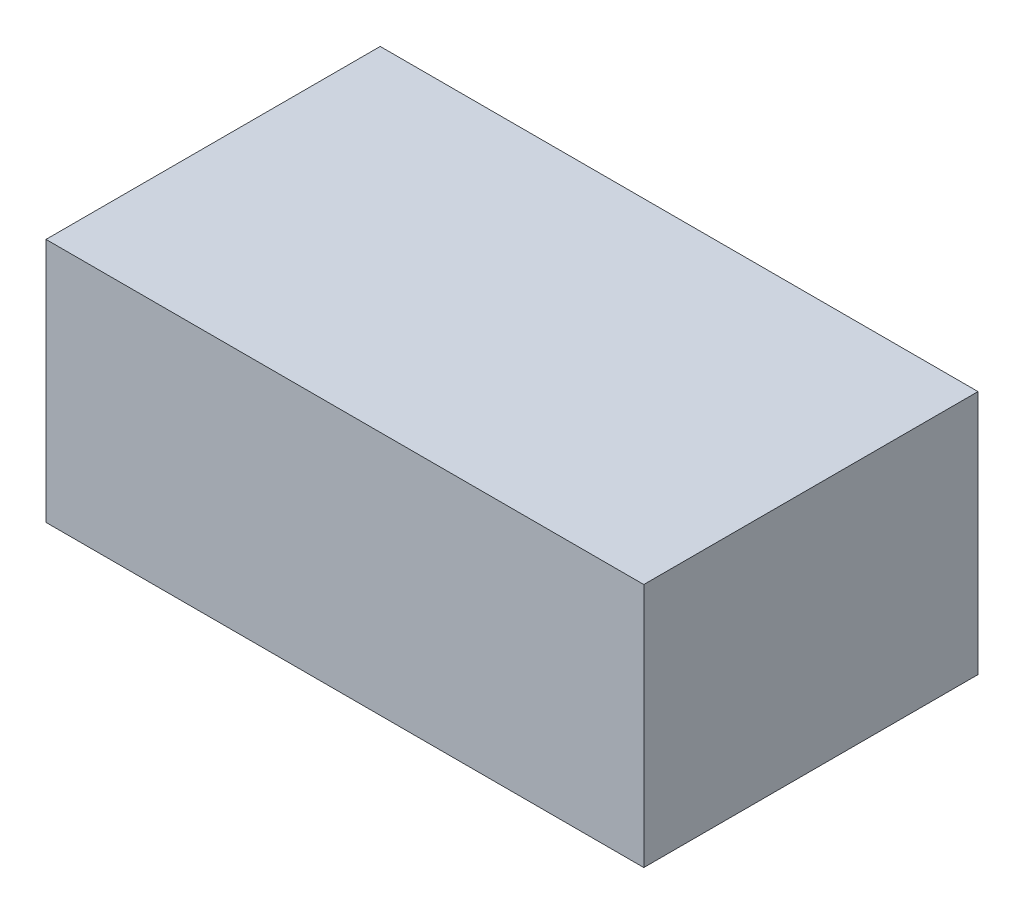
SolidWorks part; units mm, degrees
ref_plane "Front Plane" through (0, 0, 0) normal (0, 0, 1) x (1, 0, 0)
ref_plane "Top Plane" through (0, 0, 0) normal (0, 1, 0) x (1, 0, 0)
ref_plane "Right Plane" through (0, 0, 0) normal (1, 0, 0) x (0, 0, -1)
sketch "Sketch1" plane through (0, 0, 0) normal (0, 1, 0) x (1, 0, 0)
  line L1 (-14.4018, 8.0518) -> (14.4018, 8.0518)
  line L2 (-14.4018, 8.0518) -> (-14.4018, -8.0518)
  line L3 (-14.4018, -8.0518) -> (14.4018, -8.0518)
  line L4 (14.4018, 8.0518) -> (14.4018, -8.0518)
  line L5 (-14.4018, 8.0518) -> (14.4018, -8.0518) construction
  line L6 (-14.4018, -8.0518) -> (14.4018, 8.0518) construction
  point P0 (0, 0)
  dimension "D1" = 28.8036
  dimension "D2" = 16.1036
extrude "Boss-Extrude1" add sketch "Sketch1" along normal blind 11.811
